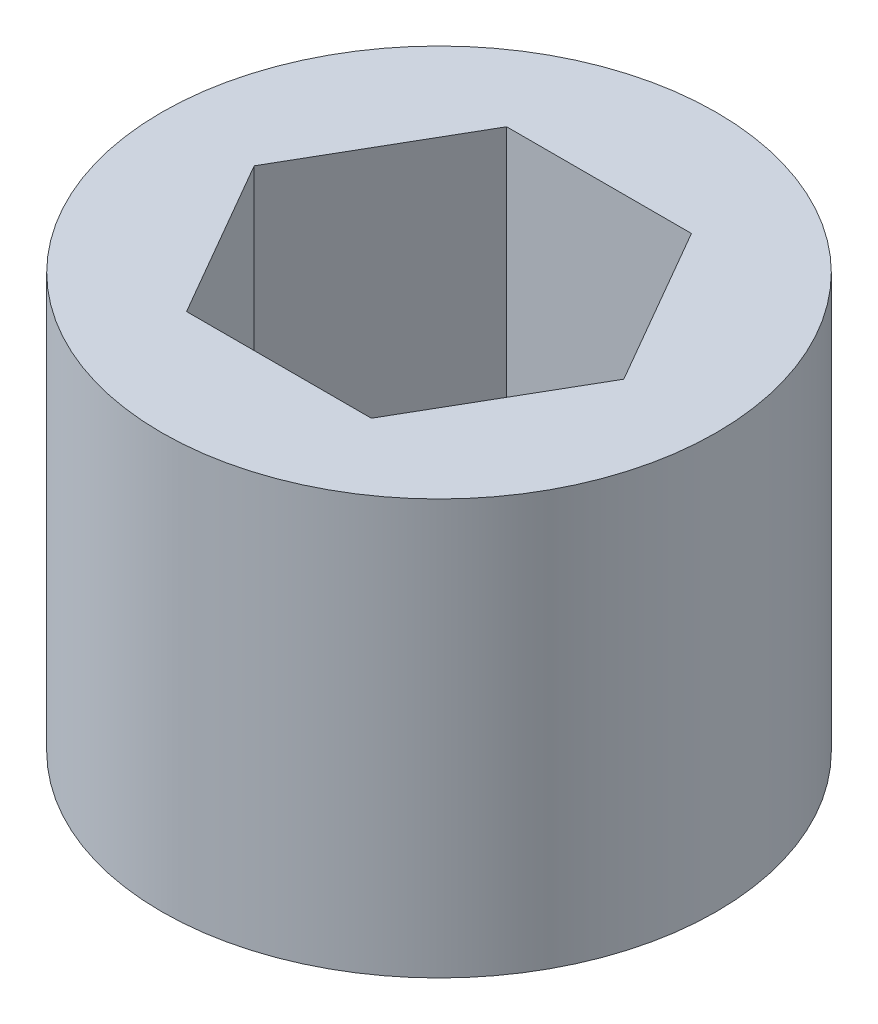
SolidWorks part; units mm, degrees
material "Markforged"
ref_plane "Front Plane" through (0, 0, 0) normal (0, 0, 1) x (1, 0, 0)
ref_plane "Top Plane" through (0, 0, 0) normal (0, 1, 0) x (1, 0, 0)
ref_plane "Right Plane" through (0, 0, 0) normal (1, 0, 0) x (0, 0, -1)
sketch "Sketch1" plane through (0, 0, 0) normal (0, 1, 0) x (1, 0, 0)
  line L1 (1.3748, -2.3813) -> (2.7496, 0)
  line L2 (2.7496, 0) -> (1.3748, 2.3812)
  line L3 (1.3748, 2.3812) -> (-1.3748, 2.3812)
  line L4 (-1.3748, 2.3812) -> (-2.7496, 0)
  line L5 (-2.7496, 0) -> (-1.3748, -2.3813)
  line L6 (-1.3748, -2.3813) -> (1.3748, -2.3813)
  circle A0 centre (0, 0) radius 4.1275
  circle A1 centre (0, 0) radius 2.3813 construction
  dimension "D1" = 8.255
  dimension "D2" = 4.7625
extrude "Boss-Extrude1" add sketch "Sketch1" along normal mid plane 6.1722
